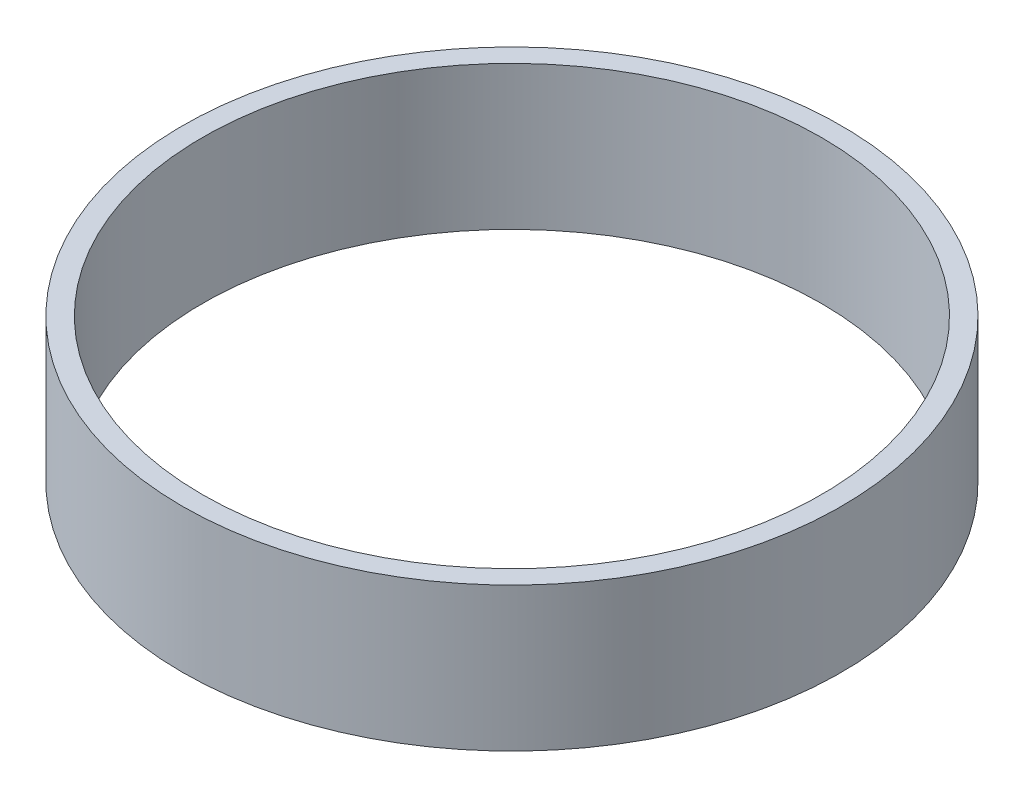
SolidWorks part; units mm, degrees
material "Hexcel AS4C (3000 Filaments)"
ref_plane "Front Plane" through (0, 0, 0) normal (0, 0, 1) x (1, 0, 0)
ref_plane "Top Plane" through (0, 0, 0) normal (0, 1, 0) x (1, 0, 0)
ref_plane "Right Plane" through (0, 0, 0) normal (1, 0, 0) x (0, 0, -1)
sketch "Sketch1" plane through (0, 0, 0) normal (0, 1, 0) x (1, 0, 0)
  circle A0 centre (0, 0) radius 27.3304
  circle A1 centre (0, 0) radius 29.1084
  dimension "D1" = 54.6608
  dimension "D2" = 1.778
extrude "Boss-Extrude1" add sketch "Sketch1" along normal blind 12.7
